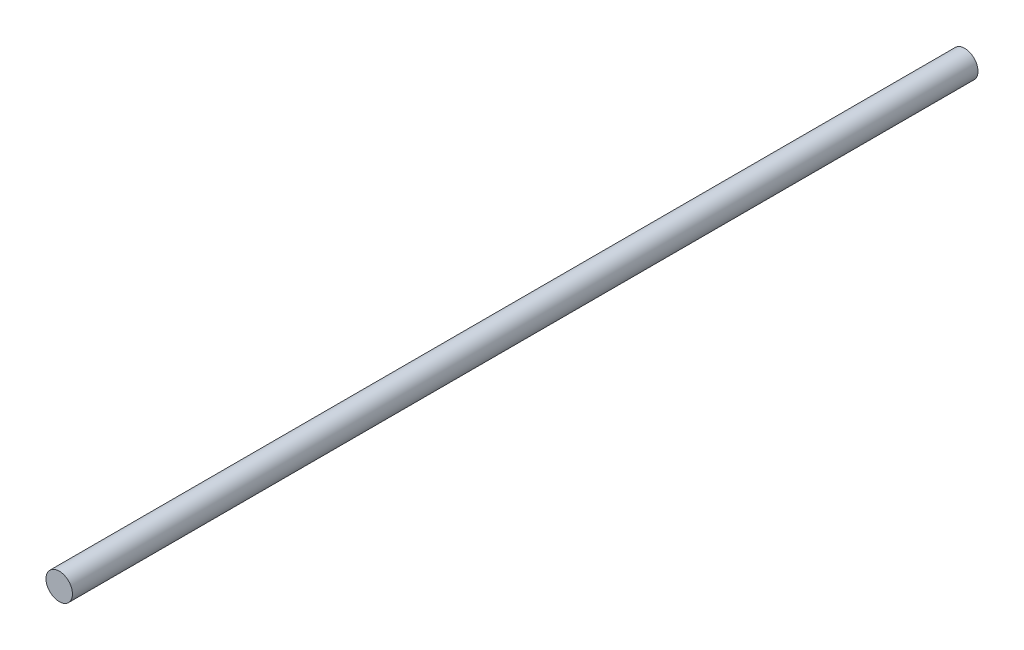
SolidWorks part; units mm, degrees
ref_plane "Front Plane" through (0, 0, 0) normal (0, 0, 1) x (1, 0, 0)
ref_plane "Top Plane" through (0, 0, 0) normal (0, 1, 0) x (1, 0, 0)
ref_plane "Right Plane" through (0, 0, 0) normal (1, 0, 0) x (0, 0, -1)
sketch "Sketch1" plane through (0, 0, 0) normal (0, 0, 1) x (1, 0, 0)
  circle A0 centre (0, 0) radius 3.95
  dimension "D1" = 7.9
extrude "Boss-Extrude1" add sketch "Sketch1" along normal blind 270
